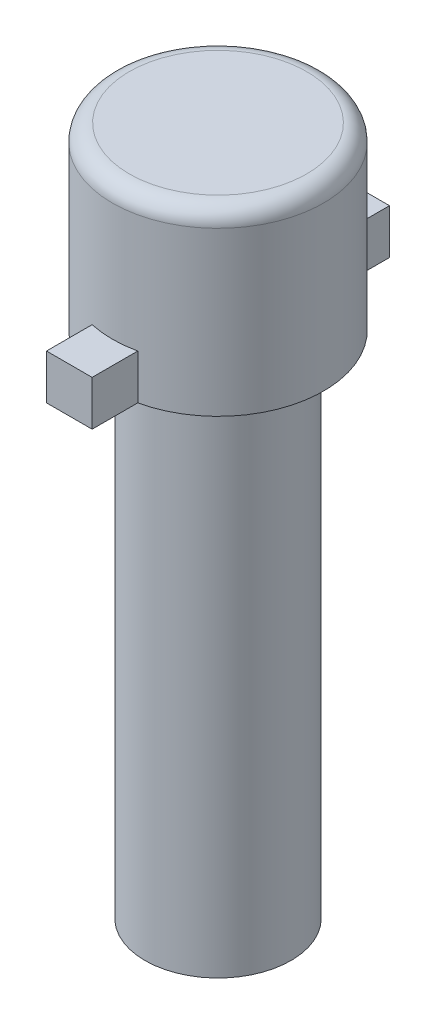
SolidWorks part; units mm, degrees
ref_plane "Front Plane" through (0, 0, 0) normal (0, 0, 1) x (1, 0, 0)
ref_plane "Top Plane" through (0, 0, 0) normal (0, 1, 0) x (1, 0, 0)
ref_plane "Right Plane" through (0, 0, 0) normal (1, 0, 0) x (0, 0, -1)
sketch "Sketch1" plane through (0, 0, 0) normal (0, 1, 0) x (1, 0, 0)
  circle A0 centre (0, 0) radius 3.25
  dimension "D1" = 6.5
extrude "Boss-Extrude1" add sketch "Sketch1" along normal blind 22.686 contours A0
sketch "Sketch2" plane through (0, 0, 0) normal (0, -1, 0) x (1, 0, 0)
  circle A1 centre (0, 0) radius 1.75
  dimension "D1" = 3.5
extrude "Cut-Extrude1" [suppressed] cut sketch "Sketch2" against normal blind 3.35
sketch "Sketch6" plane through (0, 22.686, 0) normal (0, 1, 0) x (1, 0, 0)
  circle A0 centre (0, 0) radius 4.7
  dimension "D1" = 9.4
extrude "Boss-Extrude2" add sketch "Sketch6" along normal blind 8 contours A0
fillet "Fillet1" radius 0.75 1 edges at (0, 30.686, 4.7)
sketch "Sketch7" plane through (0, 22.686, 0) normal (0, -1, 0) x (1, 0, 0)
  line L0 (0, 4.7) -> (0, -4.7) construction
  line L1 (-1.016, 4.5889) -> (-1.016, 6.6209)
  line L2 (-1.016, 6.6209) -> (1.016, 6.6209)
  line L3 (1.016, 6.6209) -> (1.016, 4.5889)
  line L4 (-4.7, 0) -> (4.7, 0) construction
  line L5 (1.016, -6.6209) -> (1.016, -4.5889)
  line L6 (-1.016, -6.6209) -> (1.016, -6.6209)
  line L7 (-1.016, -4.5889) -> (-1.016, -6.6209)
  circle A0 centre (0, 0) radius 4.7 construction
  arc A1 (1.016, -4.5889) -> (-1.016, -4.5889) centre (0, 0) cw
  circle A2 centre (0, 0) radius 4.7
  arc A3 (1.016, 4.5889) -> (-1.016, 4.5889) centre (0, 0) ccw
  dimension "D1" = 2.032
  dimension "D2" = 2.032
  dimension "D3" = 0
extrude "Boss-Extrude3" add sketch "Sketch7" against normal blind 2
